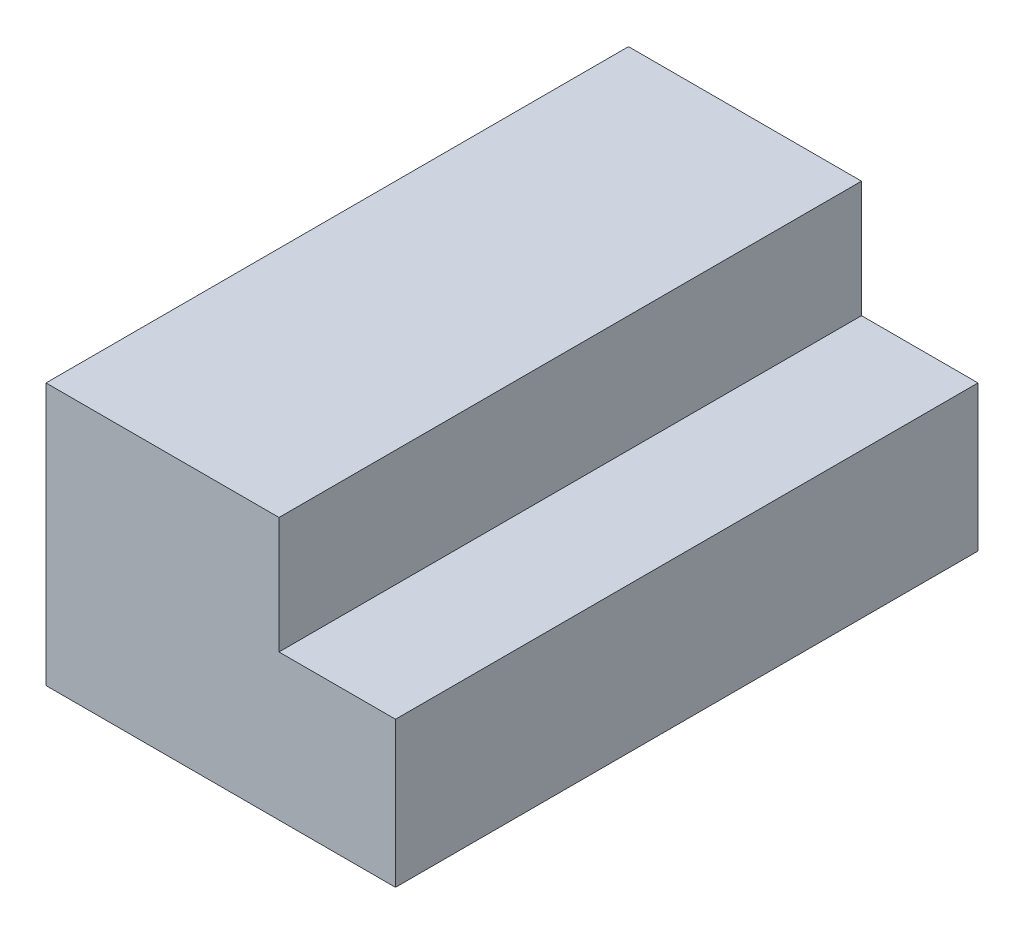
SolidWorks part; units mm, degrees
ref_plane "Front Plane" through (0, 0, 0) normal (0, 0, 1) x (1, 0, 0)
ref_plane "Top Plane" through (0, 0, 0) normal (0, 1, 0) x (1, 0, 0)
ref_plane "Right Plane" through (0, 0, 0) normal (1, 0, 0) x (0, 0, -1)
sketch "Sketch1" plane through (0, 0, 0) normal (0, 0, 1) x (1, 0, 0)
  line L0 (-2, 1) -> (0, 1)
  line L1 (0, 1) -> (0, 0)
  line L2 (0, 0) -> (1, 0)
  line L3 (1, 0) -> (1, -1.25)
  line L4 (1, -1.25) -> (-2, -1.25)
  line L5 (-2, -1.25) -> (-2, 1)
  dimension "D1" = 3
  dimension "D2" = 2
  dimension "D3" = 2.25
  dimension "D4" = 1
extrude "Boss-Extrude1" add sketch "Sketch1" along normal blind 5
